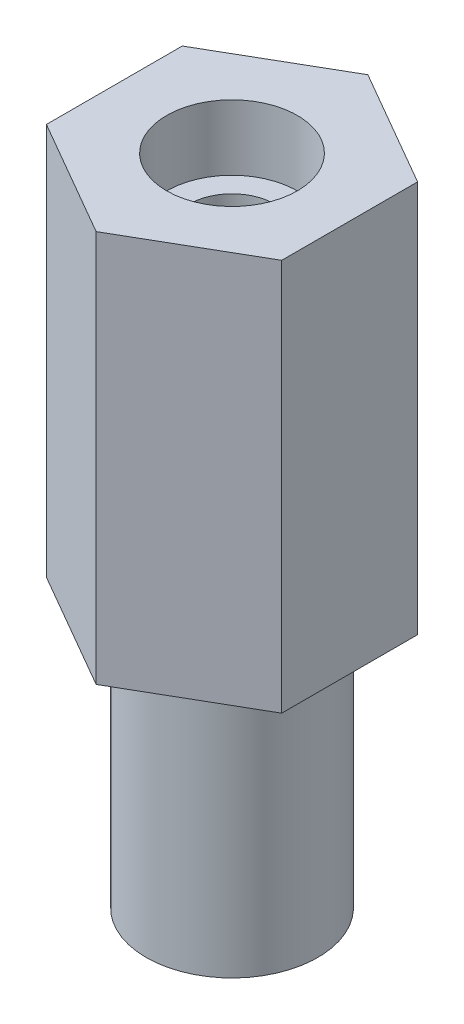
SolidWorks part; units mm, degrees
ref_plane "Спереди" through (0, 0, 0) normal (0, 0, 1) x (1, 0, 0)
ref_plane "Сверху" through (0, 0, 0) normal (0, 1, 0) x (1, 0, 0)
ref_plane "Справа" through (0, 0, 0) normal (1, 0, 0) x (0, 0, -1)
sketch "Эскиз1" plane through (0, 0, 0) normal (0, 1, 0) x (1, 0, 0)
  line L1 (0, 10.3923) -> (-9, 5.1962)
  line L2 (-9, 5.1962) -> (-9, -5.1962)
  line L3 (-9, -5.1962) -> (0, -10.3923)
  line L4 (0, -10.3923) -> (9, -5.1962)
  line L5 (9, -5.1962) -> (9, 5.1962)
  line L6 (9, 5.1962) -> (0, 10.3923)
  circle A0 centre (0, 0) radius 9 construction
  circle A1 centre (0, 0) radius 3.2644
extrude "Бобышка-Вытянуть1" add sketch "Эскиз1" along normal blind 50
sketch "Эскиз2" plane through (0, 0, 0) normal (0, -1, 0) x (1, 0, 0)
  circle A0 centre (0, 0) radius 6.5679
extrude "Вырез-Вытянуть1" cut sketch "Эскиз2" against normal blind 20 flip side to cut
sketch "Эскиз3" plane through (0, 50, 0) normal (0, 1, 0) x (1, 0, 0)
  circle A0 centre (0, 0) radius 5
extrude "Вырез-Вытянуть2" cut sketch "Эскиз3" against normal blind 5
